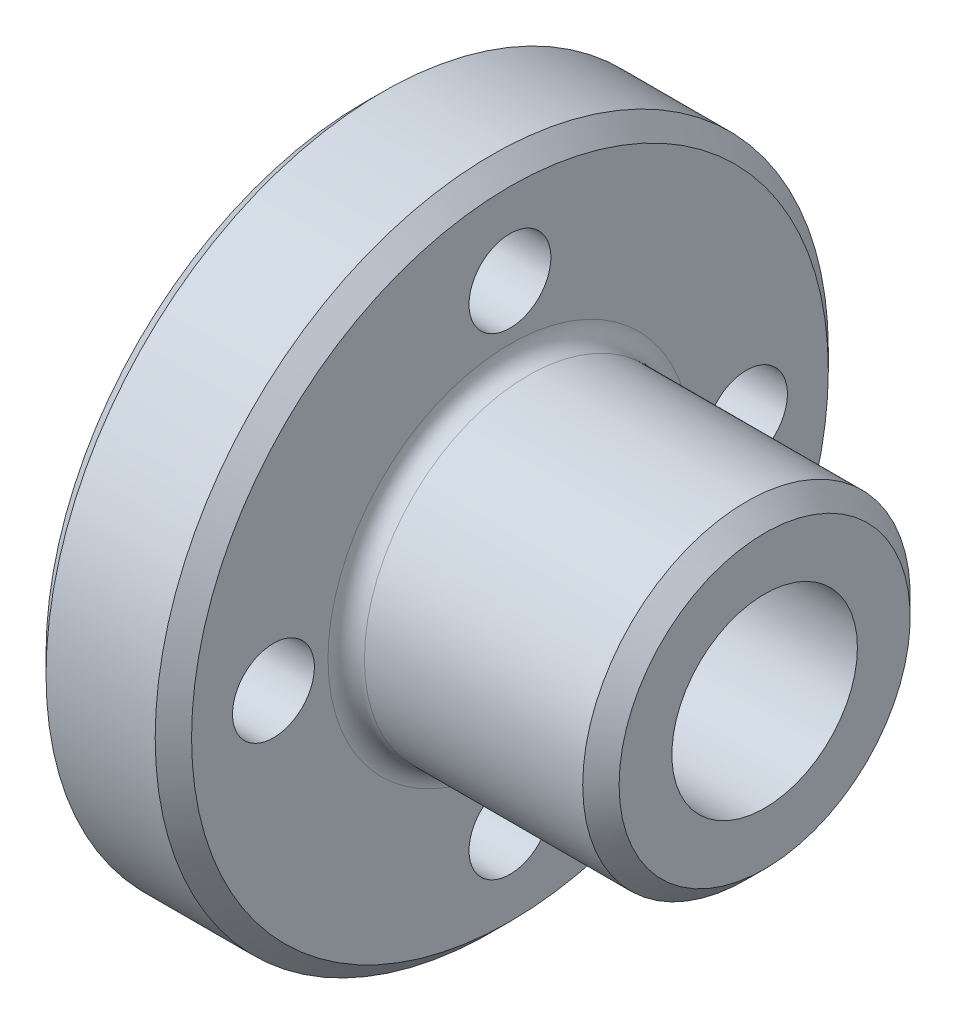
SolidWorks part; units mm, degrees
material "Nylon 6/10"
ref_plane "Piano frontale" through (0, 0, 0) normal (0, 0, 1) x (1, 0, 0)
ref_plane "Piano superiore" through (0, 0, 0) normal (0, 1, 0) x (1, 0, 0)
ref_plane "Piano destro" through (0, 0, 0) normal (1, 0, 0) x (0, 0, -1)
ref_plane "Piano1" through (0, 0, 0) normal (0, 0, 1) x (1, 0, 0)
sketch "Schizzo1" plane through (0, 0, 0) normal (0, 0, 1) x (1, 0, 0)
  line L0 (0, 0) -> (0, 18.5)
  line L2 (0, 18.5) -> (8, 18.5)
  line L4 (8, 18.5) -> (8, 9)
  line L5 (8, 9) -> (22, 9)
  line L7 (22, 9) -> (22, 0)
  line L8 (22, 0) -> (0, 0)
  line L9 (22, 0) -> (0, 0) construction
  line L10 (32.8113, 0) -> (-5.9896, 0) construction
  dimension "D1" = 37
  dimension "D2" = 18
  dimension "D3" = 8
  dimension "D4" = 22
revolve "Rivoluzione1" add sketch "Schizzo1" angle 360 about L9
hole_wizard "Foro lamato per Vite M4 a testa cilindrica piana-1" positions "Schizzo8" profile "Schizzo7" counterbore size "M4" standard "ISO" end condition through all
sketch "Schizzo8" plane through (0, 0, 0) normal (-1, 0, 0) x (0, 0, 1)
  point P0 (0, 13)
  dimension "D1" = 13
sketch "Schizzo7" plane through (0, 13, 0) normal (0, 1, 0) x (0, 0, 1)
  line L0 (0, 0) -> (0, 22)
  line L1 (0, 22) -> (2.25, 22)
  line L3 (2.25, 22) -> (2.25, 2.6)
  line L4 (2.25, 2.6) -> (4, 2.6)
  line L5 (4, 2.6) -> (4, 0)
  line L7 (4, 0) -> (0, 0)
  line L11 (0, -6.35) -> (0, 107.95) construction
  dimension "Thru Hole Dia." = 4.5
  dimension "Thru Hole Depth" = 22
  dimension "C'Bore Dia." = 8
  dimension "C'Bore Depth" = 2.6
pattern_circular "RipetizioneCircolare1" count 4 over 360 about axis through (0, 0, 0) along (1, 0, 0) of "Foro lamato per Vite M4 a testa cilindrica piana-1"
fillet "Raccordo1" radius 1 1 edges at (8, 0, 9)
chamfer "Smusso1" distance 1 angle 45 3 edges at (0, 0, 18.5) (8, 0, 18.5) (22, 0, 9)
hole_wizard "Foro filettato M12-1" positions "Schizzo10" profile "Schizzo9" tap size "M12" standard "ISO"
sketch "Schizzo10" plane through (22, 0, 0) normal (1, 0, 0) x (0, 0, -1)
  point P0 (0, 0)
sketch "Schizzo9" plane through (22, 0, 0) normal (0, 1, 0) x (0, 0, -1)
  line L0 (0, 0) -> (0, 35.8144)
  line L1 (0, 35.8144) -> (5.1, 32.75)
  line L2 (5.1, 32.75) -> (5.1, 0)
  line L5 (5.1, 0) -> (0, 0)
  line L10 (0, 35.8144) -> (-5.1, 32.75) construction
  line L11 (0, -6.35) -> (0, 107.95) construction
  dimension "Tap Drill Dia." = 10.2
  dimension "Tap Drill Depth" = 32.75
  dimension "Drill Angle" = 118
cosmetic thread "Filettatura del foro1" parameters "D1"=22, "D2"=12
chamfer "Smusso2" distance 1 angle 45 1 edges at (0, 0, -5.1)
